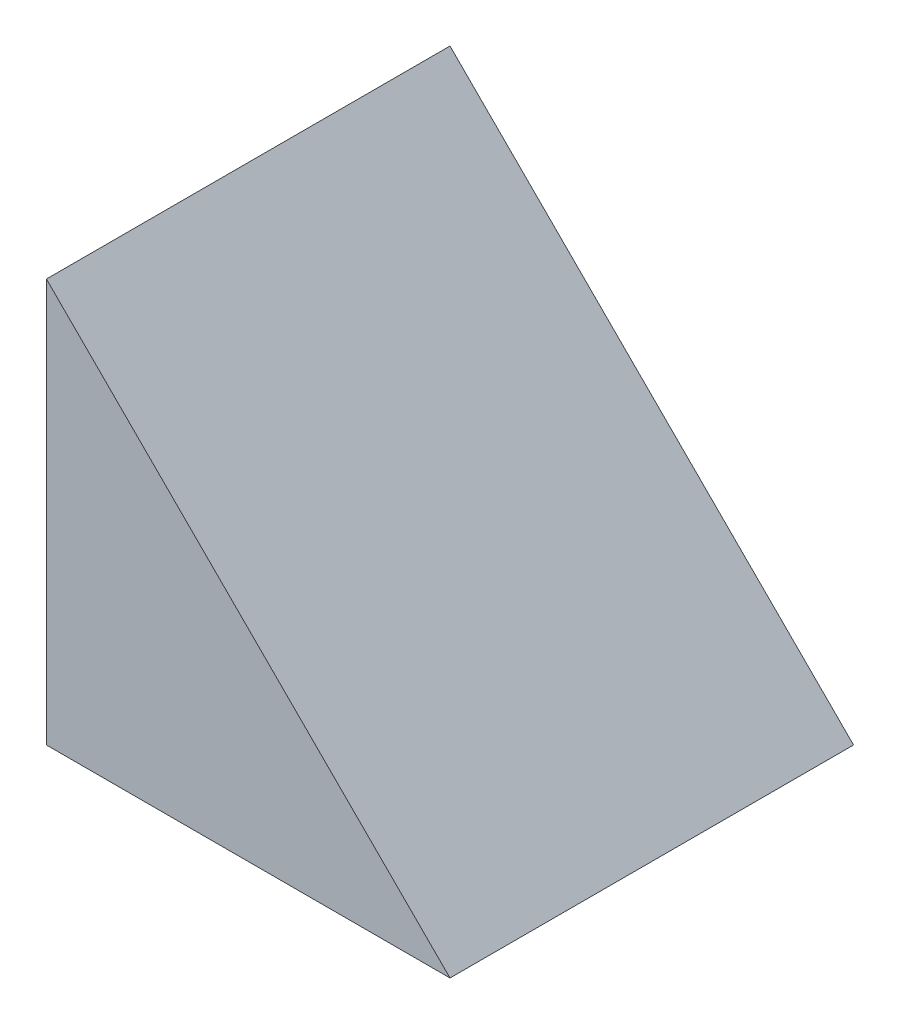
SolidWorks part; units mm, degrees
ref_plane "Front Plane" through (0, 0, 0) normal (0, 0, 1) x (1, 0, 0)
ref_plane "Top Plane" through (0, 0, 0) normal (0, 1, 0) x (1, 0, 0)
ref_plane "Right Plane" through (0, 0, 0) normal (1, 0, 0) x (0, 0, -1)
sketch "Sketch1" plane through (0, 0, 0) normal (0, 0, 1) x (1, 0, 0)
  line L0 (0, 76.2) -> (0, 0)
  line L1 (0, 0) -> (76.2, 0)
  line L2 (76.2, 0) -> (0, 76.2)
  dimension "D1" = 76.2
  dimension "D2" = 76.2
extrude "Boss-Extrude1" add sketch "Sketch1" along normal blind 76.2
equation "\"D2@Sketch1\"=\"D1@Sketch1\""
equation "\"D1@Boss-Extrude1\"=\"D1@Sketch1\""
